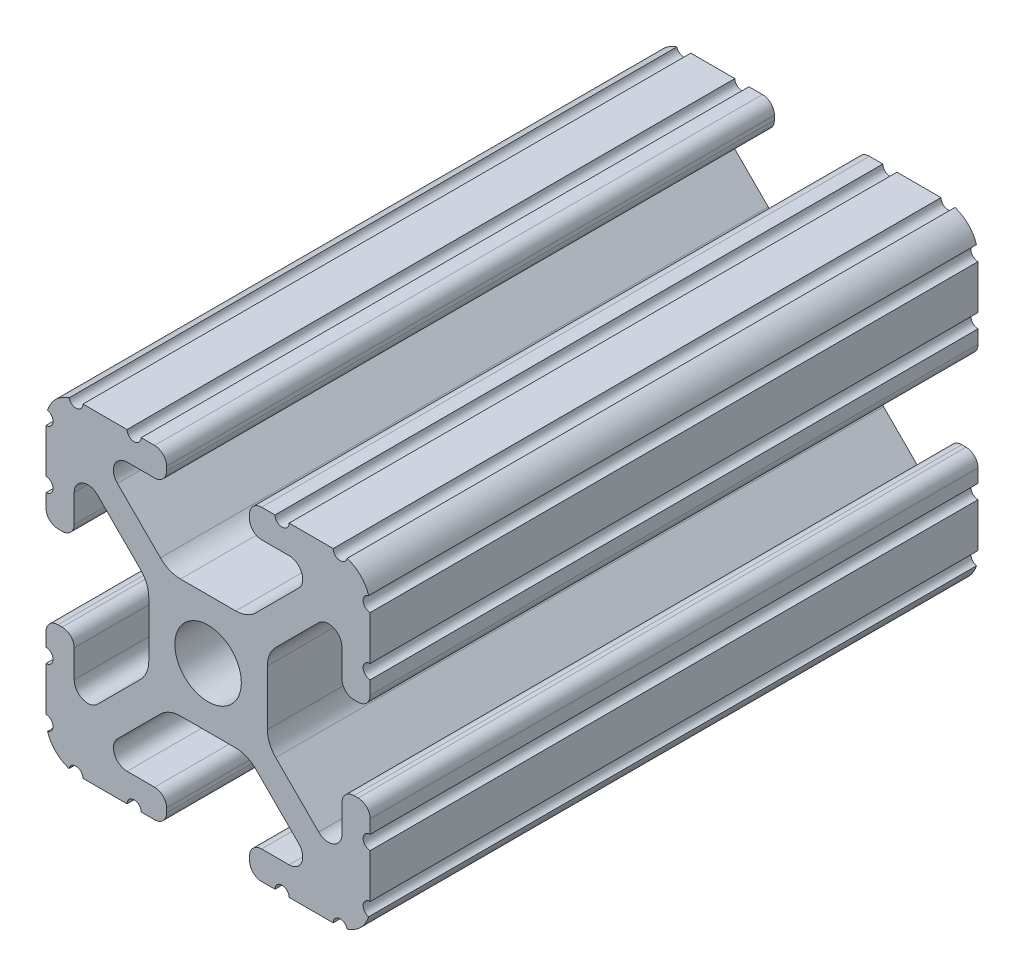
SolidWorks part; units mm, degrees
ref_plane "Front Plane" through (0, 0, 0) normal (0, 0, 1) x (1, 0, 0)
ref_plane "Top Plane" through (0, 0, 0) normal (0, 1, 0) x (1, 0, 0)
ref_plane "Right Plane" through (0, 0, 0) normal (1, 0, 0) x (0, 0, -1)
sketch "Sketch2" plane through (0, 0, 0) normal (0, 0, 1) x (1, 0, 0)
  line L0 (0, 12.7) -> (0, -12.7) construction
  line L1 (-12.7, 0) -> (12.7, 0) construction
  line L2 (3.2512, -12.7) -> (12.7, -12.7)
  line L3 (12.7, -12.7) -> (12.7, -3.2512)
  line L4 (3.2512, -12.7) -> (3.2512, -10.4902)
  line L5 (3.2512, -10.4902) -> (8.9276, -10.4902)
  line L6 (8.9276, -10.4902) -> (3.0856, -4.6482)
  line L7 (0, 0) -> (12.7, -12.7) construction
  line L8 (12.7, -3.2512) -> (10.4902, -3.2512)
  line L9 (10.4902, -3.2512) -> (10.4902, -8.9276)
  line L10 (10.4902, -8.9276) -> (4.6482, -3.0856)
  circle A0 centre (0, 0) radius 2.6035
  arc A1 (6.3485, -10.4902) -> (7.1039, -8.6665) centre (6.3485, -9.4219) ccw construction
  point P8 (0, -4.6482)
  dimension "Center Hole Diameter" = 5.207
  dimension "Rail Height" = 25.4
  dimension "Rail Width" = 25.4
  dimension "T-Slot Width" = 6.5024
  dimension "Slot Inner Width" = 14.8336
  dimension "Thickness" = 2.2098
  dimension "Slot Depth" = 5.842
  dimension "D1" = 2.2098
sketch "Sketch3" plane through (0, 0, 0) normal (1, 0, 0) x (0, 0, -1)
  line L0 (-23.8125, -12.7) -> (23.8125, -12.7) construction
  line L1 (1.5875, 0) -> (-1.5875, 0) construction
  dimension "Length" = 47.625
  dimension "D1" = 25.4
sketch "Sketch4" plane through (0, 0, 0) normal (0, 0, 1) x (1, 0, 0)
  line L0 (4.1904, -12.7) -> (10.1173, -12.7)
  line L1 (3.2512, -12.7) -> (12.7, -12.7) construction
  line L2 (3.2512, -12.7) -> (3.2512, -10.4902) construction
  line L3 (3.2512, -10.4902) -> (8.9276, -10.4902) construction
  line L4 (3.2512, -11.4294) -> (3.2512, -11.7608)
  line L5 (4.1904, -10.4902) -> (6.3485, -10.4902)
  line L6 (0, -4.6482) -> (2.164, -4.6482)
  line L7 (8.9276, -10.4902) -> (3.0856, -4.6482) construction
  line L8 (3.7373, -5.2999) -> (7.1039, -8.6665)
  line L9 (12.7, -12.7) -> (12.7, -3.2512) construction
  line L10 (10.4902, -8.9276) -> (4.6482, -3.0856) construction
  line L11 (10.4902, -3.2512) -> (10.4902, -8.9276) construction
  line L12 (10.4902, -6.3485) -> (10.4902, -4.1904)
  line L13 (12.7, -3.2512) -> (10.4902, -3.2512) construction
  line L14 (11.4294, -3.2512) -> (11.7608, -3.2512)
  line L15 (12.7, -4.1904) -> (12.7, -10.1173)
  line L16 (8.6665, -7.1039) -> (5.2999, -3.7373)
  line L17 (4.6482, 0) -> (4.6482, -2.164)
  line L18 (-12.7, 0) -> (12.7, 0) construction
  line L19 (0, -4.6482) -> (0, -2.6035)
  line L20 (0, 12.7) -> (0, -12.7) construction
  line L21 (4.6482, 0) -> (2.6035, 0)
  arc A0 (3.2512, -11.7608) -> (4.1904, -12.7) centre (4.1904, -11.7608) ccw
  arc A2 (3.2512, -11.4294) -> (4.1904, -10.4902) centre (4.1904, -11.4294) cw
  arc A3 (6.3485, -10.4902) -> (7.1039, -8.6665) centre (6.3485, -9.4219) ccw
  arc A4 (2.164, -4.6482) -> (3.7373, -5.2999) centre (2.164, -6.8732) cw
  arc A5 (10.1173, -12.7) -> (12.7, -10.1173) centre (10.1173, -10.1173) ccw
  arc A6 (8.6665, -7.1039) -> (10.4902, -6.3485) centre (9.4219, -6.3485) ccw
  arc A7 (10.4902, -4.1904) -> (11.4294, -3.2512) centre (11.4294, -4.1904) cw
  arc A8 (11.7608, -3.2512) -> (12.7, -4.1904) centre (11.7608, -4.1904) cw
  arc A9 (5.2999, -3.7373) -> (4.6482, -2.164) centre (6.8732, -2.164) cw
  circle A10 centre (0, 0) radius 2.6035 construction
  arc A11 (0, -2.6035) -> (2.6035, 0) centre (0, 0) ccw
  dimension "D1" = 2.5827
  dimension "D2" = 2.225
  dimension "D3" = 0.9392
extrude "Boss-Extrude1" add sketch "Sketch4" along normal mid plane 47.625
sketch "Sketch5" plane through (0, 0, 0) normal (0, 0, 1) x (1, 0, 0)
  line L0 (3.2512, -12.7) -> (12.7, -12.7) construction
  line L1 (4.1904, -10.4902) -> (6.3485, -10.4902) construction
  line L3 (0, 0) -> (12.7, -12.7) construction
  line L4 (6.3485, -10.4902) -> (6.3485, -12.7) construction
  line L5 (8.9276, -10.4902) -> (3.0856, -4.6482) construction
  circle A0 centre (10.3562, -12.7) radius 0.5524
  circle A1 centre (5.796, -12.7) radius 0.5524
  circle A2 centre (12.7, -10.3562) radius 0.5524
  circle A3 centre (12.7, -5.796) radius 0.5524
  point P10 (5.2694, -10.4902)
  point P12 (9.4219, -6.3485)
  dimension "D1" = 1.1049
extrude "Cut-Extrude1" cut sketch "Sketch5" against normal through all both and the other way through all
mirror "Mirror1" about plane through (0, 0, 0) normal (1, 0, 0) of bodies 137 134
mirror "Mirror2" about plane through (0, 0, 0) normal (0, 1, 0) of bodies 135
equation "\"D1@Boss-Extrude1\"=\"Length@Sketch3\""
equation "\"D1@Sketch2\"=\"Thickness@Sketch2\""
equation "\"D2@Sketch4\"=\"Slot Inner Width@Sketch2\"*0.15"
equation "\"D1@Sketch4\"=\"D3@Sketch4\"*2.75"
equation "\"D3@Sketch4\"=\"Thickness@Sketch2\"*0.425"
equation "\"D1@Sketch5\"=\"Thickness@Sketch2\"*0.5"
